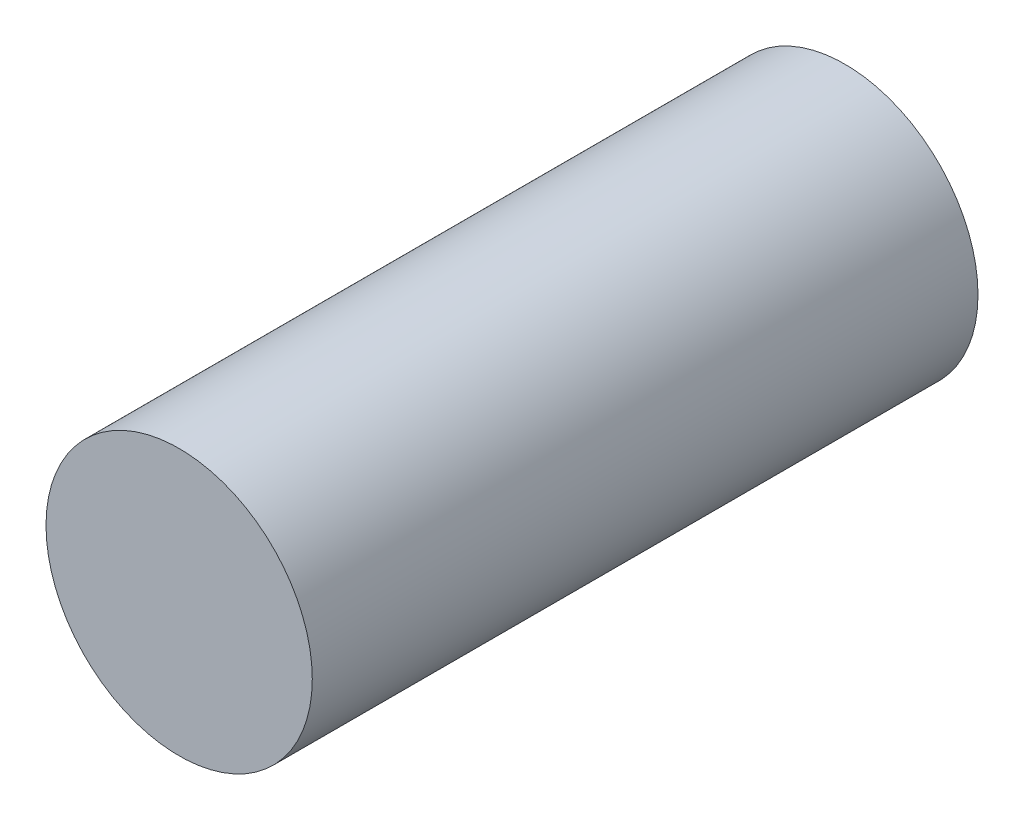
SolidWorks part; units mm, degrees
ref_plane "Front Plane" through (0, 0, 0) normal (0, 0, 1) x (1, 0, 0)
ref_plane "Top Plane" through (0, 0, 0) normal (0, 1, 0) x (1, 0, 0)
ref_plane "Right Plane" through (0, 0, 0) normal (1, 0, 0) x (0, 0, -1)
sketch "Sketch1" plane through (0, 0, 0) normal (0, 0, 1) x (1, 0, 0)
  circle A0 centre (0, 0) radius 2
extrude "Boss-Extrude1" add sketch "Sketch1" along normal blind 10
